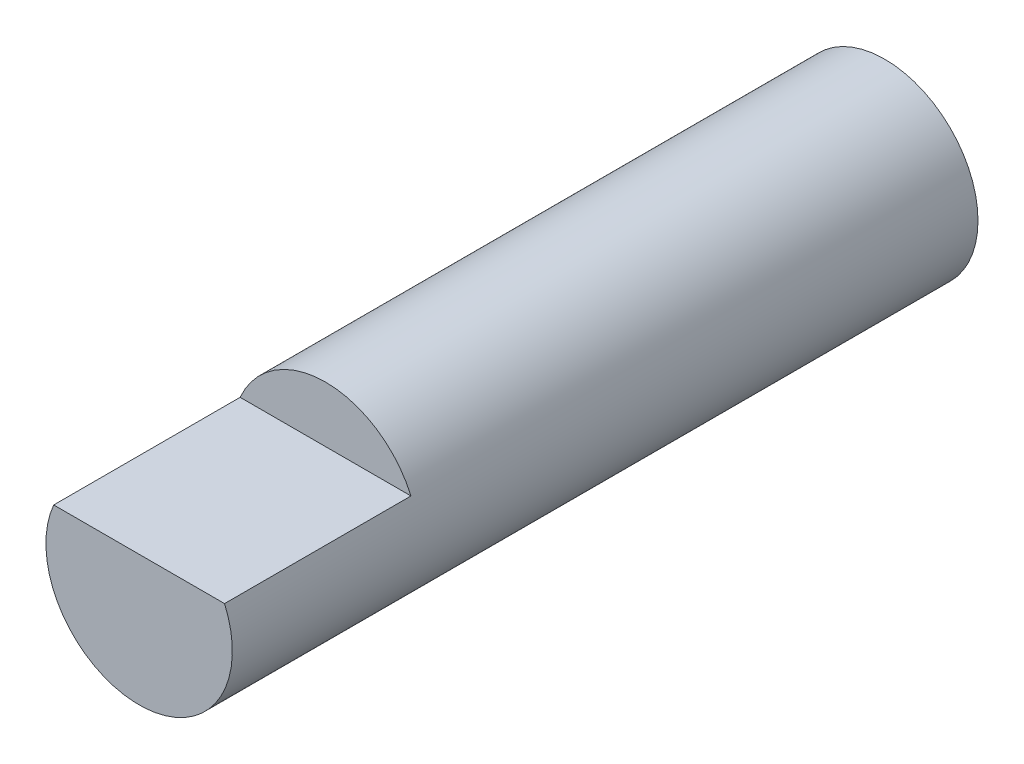
SolidWorks part; units mm, degrees
material "Plain Carbon Steel"
ref_plane "Front Plane" through (0, 0, 0) normal (0, 0, 1) x (1, 0, 0)
ref_plane "Top Plane" through (0, 0, 0) normal (0, 1, 0) x (1, 0, 0)
ref_plane "Right Plane" through (0, 0, 0) normal (1, 0, 0) x (0, 0, -1)
sketch "Sketch1" plane through (0, 0, 0) normal (0, 0, 1) x (1, 0, 0)
  circle A0 centre (0, 0) radius 3.175
  dimension "D1" = 6.35
extrude "Boss-Extrude1" add sketch "Sketch1" along normal blind 25.4
sketch "Sketch2" plane through (0, 0, 25.4) normal (0, 0, 1) x (1, 0, 0)
  line L0 (-6.35, 1.27) -> (6.35, 1.27)
  line L1 (0, -3.4925) -> (0, 3.4925) construction
  arc A0 (6.35, 1.27) -> (-6.35, 1.27) centre (0, 1.27) ccw
  circle A1 centre (0, 0) radius 3.175 construction
  dimension "D2" = 6.35
  dimension "D1" = 1.27
extrude "Cut-Extrude1" cut sketch "Sketch2" against normal blind 6.35
